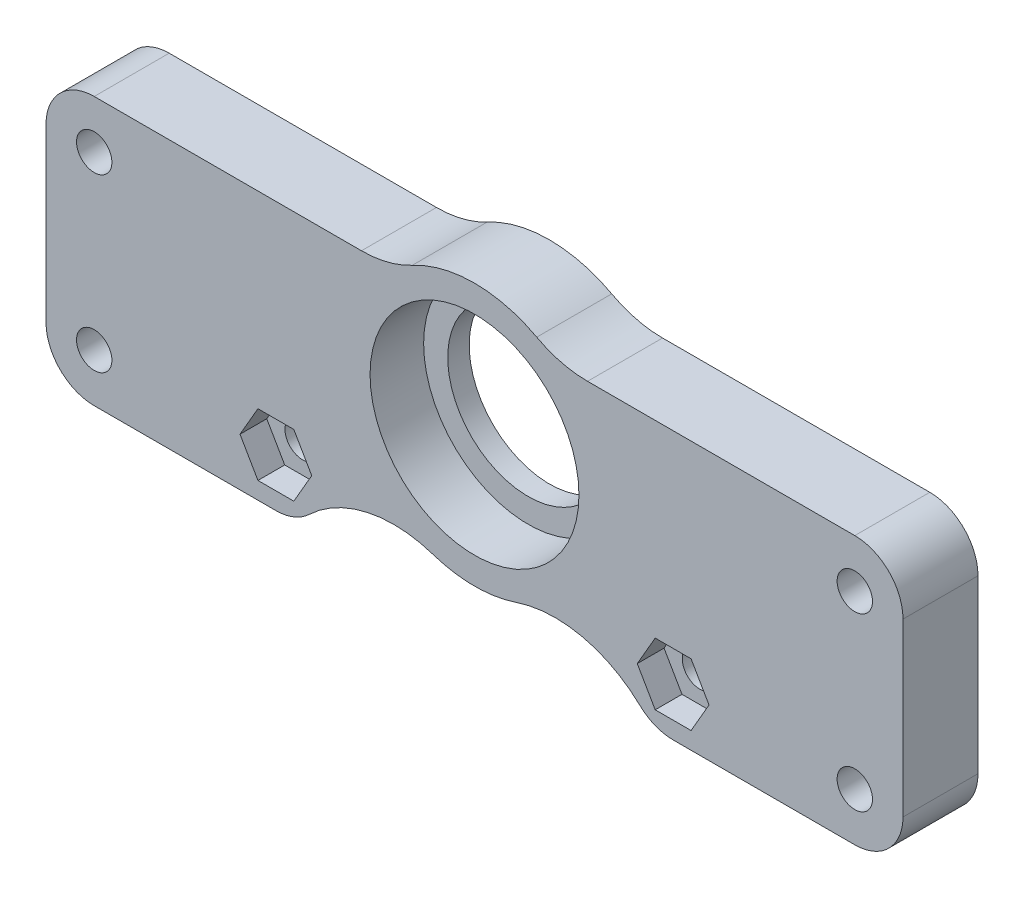
SolidWorks part; units mm, degrees
ref_plane "Front Plane" through (0, 0, 0) normal (0, 0, 1) x (1, 0, 0)
ref_plane "Top Plane" through (0, 0, 0) normal (0, 1, 0) x (1, 0, 0)
ref_plane "Right Plane" through (0, 0, 0) normal (1, 0, 0) x (0, 0, -1)
sketch "Sketch1" plane through (0, 0, 0) normal (0, 0, 1) x (1, 0, 0)
  line L0 (0, 0) -> (-40, 0) construction
  line L2 (-35.5, 9.5886) -> (-7.6237, 9.5886)
  line L3 (0, 0) -> (0, 12.25) construction
  line L6 (-18.5421, -15.4114) -> (-35.5, -15.4114)
  line L7 (-40, -10.9114) -> (-40, 5.0886)
  line L8 (35.5, 9.5886) -> (7.6237, 9.5886)
  line L9 (18.5421, -15.4114) -> (35.5, -15.4114)
  line L10 (40, -10.9114) -> (40, 5.0886)
  circle A0 centre (0, 0) radius 9.75
  arc A1 (-7.6237, 9.5886) -> (7.6237, 9.5886) centre (0, 0) cw
  arc A2 (-3.8862, -11.6172) -> (3.8862, -11.6172) centre (0, 0) ccw
  arc A3 (-3.8862, -11.6172) -> (-15.4462, -14.1772) centre (-7.5345, -22.5232) ccw
  arc A15 (-15.4462, -14.1772) -> (-18.5421, -15.4114) centre (-18.5421, -10.9114) cw
  arc A16 (-35.5, -15.4114) -> (-40, -10.9114) centre (-35.5, -10.9114) cw
  arc A17 (-40, 5.0886) -> (-35.5, 9.5886) centre (-35.5, 5.0886) cw
  circle A18 centre (-35.5, 5.0886) radius 1.65
  arc A21 (3.8862, -11.6172) -> (15.4462, -14.1772) centre (7.5345, -22.5232) cw
  arc A22 (15.4462, -14.1772) -> (18.5421, -15.4114) centre (18.5421, -10.9114) ccw
  circle A25 centre (35.5, 5.0886) radius 1.65
  arc A26 (40, 5.0886) -> (35.5, 9.5886) centre (35.5, 5.0886) ccw
  arc A27 (35.5, -15.4114) -> (40, -10.9114) centre (35.5, -10.9114) ccw
  circle A28 centre (-18.5421, -10.9114) radius 1.65
  circle A29 centre (-35.5, -10.9114) radius 1.65
  circle A30 centre (18.5421, -10.9114) radius 1.65
  circle A31 centre (35.5, -10.9114) radius 1.65
  dimension "D1" = 19.5
  dimension "D2" = 2.5
  dimension "D4" = 2.5
  dimension "D5" = 40
  dimension "D8" = 11.5
  dimension "D9" = 11.56
  dimension "D3" = 4.5
  dimension "D7" = 3.3
  dimension "D6" = 16
  dimension "D10" = 2.56
extrude "Boss-Extrude1" add sketch "Sketch1" along normal blind 7
fillet "Fillet1" radius 10 2 edges at (7.6237, 9.5886, 3.5) (-7.6237, 9.5886, 3.5)
sketch "Sketch2" plane through (0, 0, 0) normal (0, 0, 1) x (1, 0, 0)
  circle A0 centre (0, 0) radius 7.5
  circle A1 centre (0, 0) radius 9.75 construction
  circle A2 centre (0, 0) radius 9.75
  dimension "D1" = 15
extrude "Boss-Extrude2" add sketch "Sketch2" along normal blind 2
sketch "Sketch3" plane through (0, 0, 7) normal (0, 0, 1) x (1, 0, 0)
  line L1 (-16.8678, -8.0114) -> (-20.2164, -8.0114)
  line L2 (-20.2164, -8.0114) -> (-21.8907, -10.9114)
  line L3 (-21.8907, -10.9114) -> (-20.2164, -13.8114)
  line L4 (-20.2164, -13.8114) -> (-16.8678, -13.8114)
  line L5 (-16.8678, -13.8114) -> (-15.1935, -10.9114)
  line L6 (-15.1935, -10.9114) -> (-16.8678, -8.0114)
  line L7 (20.2164, -8.0114) -> (16.8678, -8.0114)
  line L8 (16.8678, -8.0114) -> (15.1935, -10.9114)
  line L9 (15.1935, -10.9114) -> (16.8678, -13.8114)
  line L10 (16.8678, -13.8114) -> (20.2164, -13.8114)
  line L11 (20.2164, -13.8114) -> (21.8907, -10.9114)
  line L12 (21.8907, -10.9114) -> (20.2164, -8.0114)
  circle A0 centre (-18.5421, -10.9114) radius 2.9 construction
  circle A1 centre (18.5421, -10.9114) radius 2.9 construction
  dimension "D1" = 5.8
extrude "Cut-Extrude1" cut sketch "Sketch3" against normal blind 2.5
sketch "Sketch4" plane through (0, 0, 0) normal (0, 0, -1) x (-1, 0, 0)
  circle A0 centre (-18.5421, -10.9114) radius 2.5
  circle A1 centre (18.5421, -10.9114) radius 2.5
  circle A2 centre (-18.5421, -10.9114) radius 1.65 construction
  circle A3 centre (18.5421, -10.9114) radius 1.65 construction
  circle A4 centre (-18.5421, -10.9114) radius 1.65
  circle A5 centre (18.5421, -10.9114) radius 1.65
  dimension "D1" = 5
extrude "Boss-Extrude3" add sketch "Sketch4" along normal blind 1.5
sketch "Sketch5" plane through (0, 0, 0) normal (0, 0, -1) x (-1, 0, 0)
  circle A0 centre (-35.5, 5.0886) radius 2.95
  circle A1 centre (-35.5, -10.9114) radius 2.95
  circle A2 centre (35.5, 5.0886) radius 2.95
  circle A3 centre (35.5, -10.9114) radius 2.95
  dimension "D1" = 5.9
extrude "Cut-Extrude2" cut sketch "Sketch5" against normal blind 3.2
